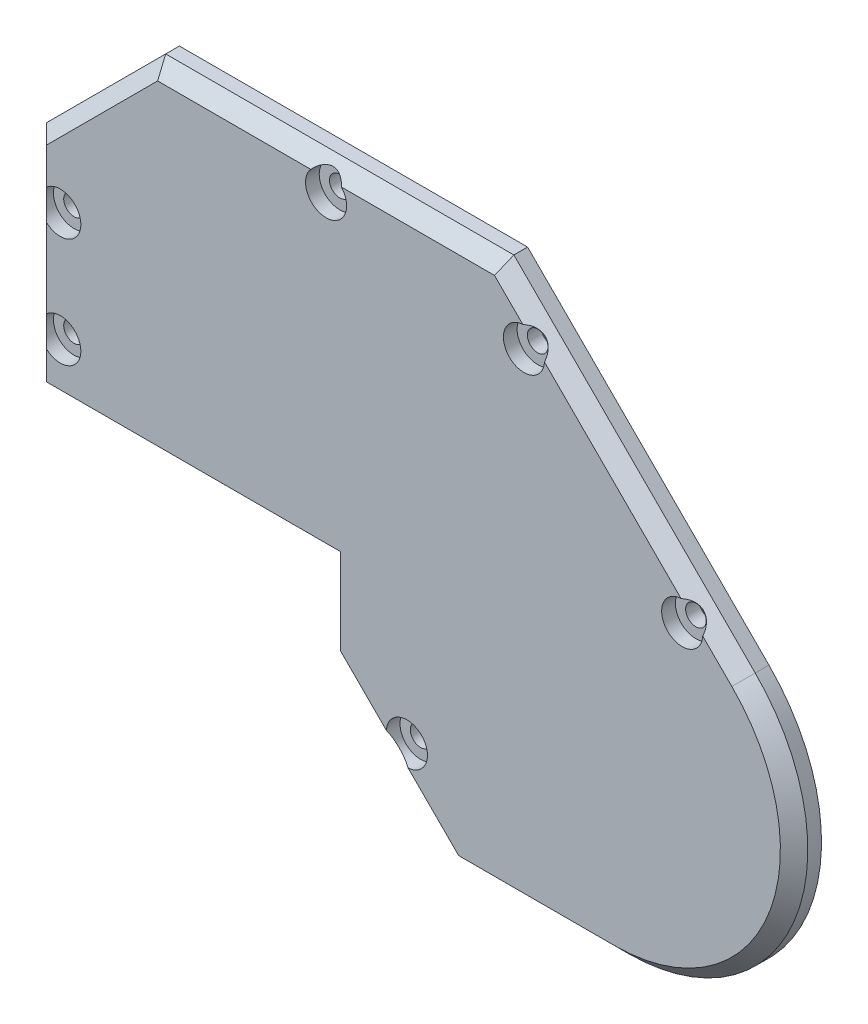
SolidWorks part; units mm, degrees
ref_plane "Plano frontal" through (0, 0, 0) normal (0, 0, 1) x (1, 0, 0)
ref_plane "Plano superior" through (0, 0, 0) normal (0, 1, 0) x (1, 0, 0)
ref_plane "Plano direito" through (0, 0, 0) normal (1, 0, 0) x (0, 0, -1)
sketch "Model" plane through (0, 0, 0) normal (0, 0, 1) x (1, 0, 0)
  line L0 (0, 0) -> (39, 0) construction
  line L1 (-0.7, 2.5) -> (39, 2.5)
  line L2 (39.7, 0) -> (39.7, -6.8548) construction
  line L3 (0, 0) -> (0, 31.4419) construction
  line L4 (50.1111, 46.949) -> (15.5071, 46.949) construction
  line L5 (0, 31.4419) -> (15.5071, 46.949) construction
  line L6 (42.2, -9.3548) -> (52.4452, -19.6) construction
  line L7 (39, -7.1448) -> (51.9502, -20.095) construction
  line L8 (97.9635, 12.6635) -> (63.6779, 46.949) construction
  line L9 (50.1111, 46.949) -> (63.6779, 46.949) construction
  line L10 (52.4452, -19.6) -> (59.4452, -26.6) construction
  line L11 (81.7, -26.6) -> (59.4452, -26.6) construction
  line L12 (-0.7, 0) -> (39, 0)
  line L13 (-0.7, 0) -> (-3.2, 0)
  line L14 (42.2, -10.3448) -> (51.9502, -20.095)
  line L15 (51.9502, -20.095) -> (59.1552, -27.3)
  line L16 (81.7, -27.3) -> (59.1552, -27.3)
  line L17 (98.4584, 13.1584) -> (63.9678, 47.649)
  line L18 (50.1111, 47.649) -> (63.9678, 47.649)
  line L19 (50.1111, 47.649) -> (15.2171, 47.649)
  line L20 (-0.7, 31.7319) -> (15.2171, 47.649)
  line L21 (-0.7, 2.5) -> (-0.7, 31.7319)
  line L22 (0, 0) -> (-0.7, 0) construction
  line L23 (38.8515, -10.5318) -> (50.1824, -21.8627) construction
  line L24 (-3.2, 0) -> (-3.2, 5)
  line L25 (-0.7, -0.7) -> (-0.7, 31.7319) construction
  line L26 (-0.7, -0.7) -> (39, -0.7) construction
  line L27 (39, -0.7) -> (39, -7.1448) construction
  line L28 (39, -0.7) -> (39, -0.7) construction
  line L29 (39, 0) -> (39.7, 0)
  line L30 (39.7, 0) -> (39.7, -11.3803)
  line L31 (39, 2.5) -> (39.7, 2.5)
  line L32 (39.7, 2.5) -> (42.2, 2.5)
  line L33 (39, 0) -> (39.7, 0) construction
  line L34 (42.2, 2.5) -> (42.2, -10.3448)
  line L35 (-3.2, 5) -> (-3.2, 32.7674)
  line L36 (-3.2, 32.7674) -> (14.1816, 50.149)
  line L37 (50.1111, 50.149) -> (14.1816, 50.149)
  line L38 (50.1111, 50.149) -> (65.0034, 50.149)
  line L39 (100.2262, 14.9262) -> (65.0034, 50.149)
  line L40 (81.7, -29.8) -> (58.1197, -29.8)
  line L41 (50.1824, -21.8627) -> (58.1197, -29.8)
  line L42 (39.7, -11.3803) -> (50.1824, -21.8627)
  line L43 (-0.7, 2.5) -> (-5.7, 2.5) construction
  line L44 (-5.7, 0) -> (-5.7, 2.5) construction
  line L45 (-0.7, 0) -> (-5.7, 0) construction
  line L46 (-3.2, 5) -> (-8.2, 5) construction
  line L47 (-8.2, -2.5) -> (-8.2, 5) construction
  line L48 (-0.7, -2.5) -> (39, -2.5) construction
  line L49 (-0.7, -2.5) -> (-8.2, -2.5) construction
  line L51 (40.6192, -8.764) -> (51.9502, -20.095) construction
  line L52 (39.7, -6.8548) -> (52.4452, -19.6) construction
  arc A0 (81.7, -27.3) -> (98.4584, 13.1584) centre (81.7, -3.6) ccw
  arc A1 (81.7, -29.8) -> (100.2262, 14.9262) centre (81.7, -3.6) ccw
  circle A2 centre (59.0726, 19.0274) radius 7.35 construction
  arc A5 (81.7, -26.6) -> (97.9635, 12.6635) centre (81.7, -3.6) ccw construction
  circle A6 centre (81.7, -3.6) radius 7.3 construction
  circle A13 centre (27.384, 23.481) radius 7.35 construction
  dimension "D2" = 2.5
  dimension "D1" = 0.7
extrude "Ressalto-extrusão1" add sketch "Model" along normal blind 48
sketch "Esboço12" plane through (57.5762, 57.5762, 0) normal (0.7071, 0.7071, 0) x (0, 0, -1)
  line L0 (-48, -35.4099) -> (-44, -35.4099) construction
  line L1 (-48, -60.3162) -> (-48, -10.5036) construction
  line L2 (-44, -35.4099) -> (-44, -43.4099) construction
  line L3 (-44, -35.4099) -> (-44, -19.4099) construction
  line L4 (-44, -19.4099) -> (-44, -51.4099) construction
  circle A0 centre (-44, -19.4099) radius 1.5
  circle A1 centre (-44, -51.4099) radius 1.5
extrude "Corte-extrusão10" cut sketch "Esboço12" against normal blind 10
sketch "Esboço13" plane through (0, 50.149, 0) normal (0, 1, 0) x (1, 0, 0)
  line L0 (39.5925, -48) -> (39.5925, -44) construction
  line L1 (65.0034, -48) -> (14.1816, -48) construction
  circle A0 centre (39.5925, -44) radius 1.5
extrude "Corte-extrusão11" cut sketch "Esboço13" against normal blind 10
sketch "Esboço14" plane through (-3.2, 0, 0) normal (-1, 0, 0) x (0, 0, 1)
  line L0 (48, 16.3837) -> (44, 16.3837) construction
  line L1 (48, 32.7674) -> (48, 0) construction
  line L2 (44, 16.3837) -> (44, 24.3837) construction
  line L3 (44, 24.3837) -> (44, 8.3837) construction
  circle A0 centre (44, 24.3837) radius 1.5
  circle A1 centre (44, 8.3837) radius 1.5
extrude "Corte-extrusão12" cut sketch "Esboço14" against normal blind 10
sketch "Esboço15" plane through (14.1598, 14.1598, 0) normal (-0.7071, -0.7071, 0) x (0, 0, 1)
  line L0 (48, -62.1686) -> (44, -62.1686) construction
  line L1 (48, -62.1686) -> (0, -62.1686) construction
  line L2 (0, -36.4548) -> (0, -50.9436) construction
  line L3 (0, -50.9436) -> (0, -60.8431) construction
  line L4 (0, -36.4548) -> (0, -50.9436) construction
  line L5 (0, -50.9436) -> (0, -60.8431) construction
  line L6 (0, -60.8431) -> (0, -36.4548) construction
  line L7 (0, -36.4548) -> (0, -48.6489) construction
  line L8 (0, -48.6489) -> (48, -48.6489) construction
  line L9 (48, -36.1192) -> (48, -62.1686) construction
  line L10 (48, -48.6489) -> (44, -48.6489) construction
  circle A0 centre (44, -48.6489) radius 1.5
extrude "Corte-extrusão13" cut sketch "Esboço15" against normal blind 10
sketch "Esboço16" plane through (0, 0, 48) normal (0, 0, 1) x (1, 0, 0)
  line L0 (39.7, 0) -> (39.7, -2)
  line L4 (42.2, -2) -> (42.2, 2.5)
  line L5 (42.2, 2.5) -> (-0.7, 2.5)
  line L6 (39.7, 0) -> (39.7, -2) construction
  line L8 (39.7, -2) -> (42.2, -2)
  line L12 (-0.7, 0) -> (39.7, 0)
  line L13 (-0.7, 2.5) -> (-0.7, 0)
extrude "Corte-extrusão14" cut sketch "Esboço16" against normal blind 10
sketch "Esboço17" plane through (0, 0, 0) normal (0, 0, -1) x (-1, 0, 0)
  line L0 (-92.8678, 22.2846) -> (-94.9892, 20.1632) construction
  line L1 (-92.8678, 22.2846) -> (-94.9892, 20.1632) construction
  line L2 (-70.2404, 44.912) -> (-72.3617, 42.7907) construction
  line L3 (-70.2404, 44.912) -> (-72.3617, 42.7907) construction
  line L4 (-38.0925, 50.149) -> (-41.0925, 50.149) construction
  line L5 (-38.0925, 50.149) -> (-41.0925, 50.149) construction
  line L6 (3.2, 22.8837) -> (3.2, 25.8837) construction
  line L7 (3.2, 22.8837) -> (3.2, 25.8837) construction
  line L8 (3.2, 6.8837) -> (3.2, 9.8837) construction
  line L9 (3.2, 6.8837) -> (3.2, 9.8837) construction
  line L10 (-49.6205, -21.3008) -> (-47.4992, -19.1795) construction
  line L11 (-49.6205, -21.3008) -> (-47.4992, -19.1795) construction
  line L12 (-93.9285, 21.2239) -> (-91.1001, 18.3955) construction
  line L13 (-71.3011, 43.8513) -> (-68.4727, 41.0229) construction
  line L14 (-39.5925, 50.149) -> (-39.5925, 46.149) construction
  line L15 (3.2, 24.3837) -> (-0.8, 24.3837) construction
  line L16 (3.2, 8.3837) -> (-0.8, 8.3837) construction
  line L17 (-48.5598, -20.2402) -> (-51.3883, -17.4117) construction
  line L18 (-69.8727, 39.6229) -> (-67.0727, 39.6229)
  line L19 (-92.5001, 19.7955) -> (-89.7001, 19.7955)
  line L20 (-92.5001, 19.7955) -> (-92.5001, 16.9955)
  line L21 (-92.5001, 16.9955) -> (-89.7001, 16.9955)
  line L22 (-89.7001, 19.7955) -> (-89.7001, 16.9955)
  line L23 (-92.5001, 19.7955) -> (-89.7001, 16.9955) construction
  line L24 (-92.5001, 16.9955) -> (-89.7001, 19.7955) construction
  line L25 (-69.8727, 39.6229) -> (-67.0727, 42.4229) construction
  line L26 (-69.8727, 42.4229) -> (-67.0727, 39.6229) construction
  line L27 (-69.8727, 42.4229) -> (-69.8727, 39.6229)
  line L28 (-69.8727, 42.4229) -> (-67.0727, 42.4229)
  line L29 (-67.0727, 42.4229) -> (-67.0727, 39.6229)
  line L30 (-38.1925, 47.549) -> (-38.1925, 44.749)
  line L31 (-40.9925, 44.749) -> (-38.1925, 47.549) construction
  line L32 (-40.9925, 47.549) -> (-40.9925, 44.749)
  line L33 (-40.9925, 47.549) -> (-38.1925, 44.749) construction
  line L34 (-40.9925, 44.749) -> (-38.1925, 44.749)
  line L35 (-40.9925, 47.549) -> (-38.1925, 47.549)
  line L36 (-2.2, 25.7837) -> (0.6, 22.9837) construction
  line L37 (-2.2, 22.9837) -> (0.6, 22.9837)
  line L38 (0.6, 25.7837) -> (0.6, 22.9837)
  line L39 (-2.2, 25.7837) -> (0.6, 25.7837)
  line L40 (-2.2, 22.9837) -> (0.6, 25.7837) construction
  line L41 (-2.2, 25.7837) -> (-2.2, 22.9837)
  line L42 (0.6, 9.7837) -> (0.6, 6.9837)
  line L43 (-2.2, 9.7837) -> (0.6, 9.7837)
  line L44 (-2.2, 6.9837) -> (0.6, 6.9837)
  line L45 (-2.2, 9.7837) -> (0.6, 6.9837) construction
  line L46 (-2.2, 9.7837) -> (-2.2, 6.9837)
  line L47 (-2.2, 6.9837) -> (0.6, 9.7837) construction
  line L48 (-52.7883, -18.8117) -> (-49.9883, -18.8117)
  line L49 (-52.7883, -16.0117) -> (-49.9883, -18.8117) construction
  line L50 (-52.7883, -18.8117) -> (-49.9883, -16.0117) construction
  line L51 (-52.7883, -16.0117) -> (-49.9883, -16.0117)
  line L52 (-49.9883, -16.0117) -> (-49.9883, -18.8117)
  line L53 (-52.7883, -16.0117) -> (-52.7883, -18.8117)
  circle A0 centre (-91.1001, 18.3955) radius 4
  circle A1 centre (-68.4727, 41.0229) radius 4
  circle A2 centre (-39.5925, 46.149) radius 4
  circle A3 centre (-0.8, 24.3837) radius 4
  circle A4 centre (-0.8, 8.3837) radius 4
  circle A5 centre (-51.3883, -17.4117) radius 4
extrude "Ressalto-extrusão2" add sketch "Esboço17" against normal blind 4
sketch "Esboço18" plane through (0, 0, 0) normal (0, 0, -1) x (-1, 0, 0)
  line L0 (-65.0034, 50.149) -> (-14.1816, 50.149) construction
  line L1 (-100.2262, 14.9262) -> (-65.0034, 50.149) construction
  line L2 (-14.1816, 50.149) -> (3.2, 32.7674) construction
  line L3 (3.2, 32.7674) -> (3.2, 0) construction
  line L4 (3.2, 0) -> (-39.7, 0) construction
  line L5 (-39.7, 0) -> (-39.7, -11.3803) construction
  line L6 (-39.7, -11.3803) -> (-58.1197, -29.8) construction
  line L7 (-58.1197, -29.8) -> (-81.7, -29.8) construction
  line L8 (-65.0034, 50.149) -> (-14.1816, 50.149)
  line L9 (-100.2262, 14.9262) -> (-65.0034, 50.149)
  line L10 (-14.1816, 50.149) -> (3.2, 32.7674)
  line L11 (3.2, 32.7674) -> (3.2, 0)
  line L12 (3.2, 0) -> (-39.7, 0)
  line L13 (-39.7, 0) -> (-39.7, -11.3803)
  line L14 (-39.7, -11.3803) -> (-58.1197, -29.8)
  line L15 (-58.1197, -29.8) -> (-81.7, -29.8)
  line L16 (-90.1687, 16.5268) -> (-90.1687, 19.3268) construction
  line L17 (-90.1687, 19.3268) -> (-92.29, 19.3268) construction
  line L18 (-90.1687, 16.5268) -> (-90.1687, 19.3268) construction
  line L19 (-90.1687, 19.3268) -> (-92.29, 19.3268) construction
  line L20 (-90.1687, 16.5268) -> (-92.6294, 18.9875) construction
  line L21 (-92.9687, 18.6482) -> (-92.29, 19.3268) construction
  line L22 (-90.1687, 19.3268) -> (-92.9687, 16.5268) construction
  arc A0 (-100.2262, 14.9262) -> (-81.7, -29.8) centre (-81.7, -3.6) ccw construction
  arc A1 (-100.2262, 14.9262) -> (-81.7, -29.8) centre (-81.7, -3.6) ccw
  circle A2 centre (-91.5687, 17.9268) radius 1.5
  circle A3 centre (-68.4727, 41.0229) radius 1.5
  circle A4 centre (-39.5925, 46.149) radius 1.5
  circle A5 centre (-0.8, 24.3837) radius 1.5
  circle A6 centre (-51.3883, -17.4117) radius 1.5
  circle A7 centre (-0.8, 8.3837) radius 1.5
extrude "Ressalto-extrusão3" add sketch "Esboço18" along normal blind 4
chamfer "Chanfro1" distance 2 angle 45 9 edges at (39.5925, 50.149, -4) (5.4908, 41.4582, -4) (-3.2, 16.3837, -4) (18.25, 0, -4) (39.7, -5.6902, -4) (48.9098, -20.5902, -4) (69.9098, -29.8, -4) (105.9056, -13.6263, -4) (82.6148, 32.5376, -4)
sketch "Esboço19" plane through (0, 0, 48) normal (0, 0, 1) x (1, 0, 0)
  line L8 (65.0034, 50.149) -> (14.1816, 50.149)
  line L9 (14.1816, 50.149) -> (-3.2, 32.7674)
  line L10 (-3.2, 32.7674) -> (-3.2, 0)
  line L11 (-3.2, 0) -> (39.7, 0)
  line L12 (39.7, 0) -> (39.7, -11.3803)
  line L13 (39.7, -11.3803) -> (58.1197, -29.8)
  line L14 (58.1197, -29.8) -> (81.7, -29.8)
  line L15 (100.2262, 14.9262) -> (65.0034, 50.149)
  line L16 (65.0034, 50.149) -> (14.1816, 50.149)
  line L17 (14.1816, 50.149) -> (-3.2, 32.7674)
  line L18 (-3.2, 32.7674) -> (-3.2, 0)
  line L19 (-3.2, 0) -> (39.7, 0)
  line L20 (39.7, 0) -> (39.7, -11.3803)
  line L21 (39.7, -11.3803) -> (58.1197, -29.8)
  line L22 (58.1197, -29.8) -> (81.7, -29.8)
  line L23 (100.2262, 14.9262) -> (65.0034, 50.149)
  arc A5 (81.7, -29.8) -> (100.2262, 14.9262) centre (81.7, -3.6) ccw
  arc A6 (81.7, -29.8) -> (100.2262, 14.9262) centre (81.7, -3.6) ccw
  dimension "D3" = 0
extrude "Corte-extrusão15" cut sketch "Esboço19" against normal up to surface (48 mm away) up to face at (43.9312, 14.8678, 0)
sketch "Esboço20" plane through (0, 0, -4) normal (0, 0, -1) x (-1, 0, 0)
  circle A0 centre (-0.8, 24.3837) radius 3
  circle A1 centre (-0.8, 8.3837) radius 3
  circle A2 centre (-39.5925, 46.149) radius 3
  circle A3 centre (-68.4727, 41.0229) radius 3
  circle A4 centre (-51.3883, -17.4117) radius 3
  circle A5 centre (-91.5687, 17.9268) radius 3
extrude "Corte-extrusão16" cut sketch "Esboço20" against normal blind 2
sketch "Esboço21" plane through (0, 0, 0) normal (0, 0, 1) x (1, 0, 0)
  line L8 (100.2262, 14.9262) -> (65.0034, 50.149)
  line L9 (65.0034, 50.149) -> (14.1816, 50.149)
  line L10 (14.1816, 50.149) -> (-3.2, 32.7674)
  line L11 (-3.2, 32.7674) -> (-3.2, 0)
  line L12 (-3.2, 0) -> (39.7, 0)
  line L13 (39.7, 0) -> (39.7, -11.3803)
  line L14 (39.7, -11.3803) -> (58.1197, -29.8)
  line L15 (58.1197, -29.8) -> (81.7, -29.8)
  line L16 (100.2262, 14.9262) -> (65.0034, 50.149)
  line L17 (65.0034, 50.149) -> (14.1816, 50.149)
  line L18 (14.1816, 50.149) -> (-3.2, 32.7674)
  line L19 (-3.2, 32.7674) -> (-3.2, 0)
  line L20 (-3.2, 0) -> (39.7, 0)
  line L21 (39.7, 0) -> (39.7, -11.3803)
  line L22 (39.7, -11.3803) -> (58.1197, -29.8)
  line L23 (58.1197, -29.8) -> (81.7, -29.8)
  arc A1 (81.7, -29.8) -> (100.2262, 14.9262) centre (81.7, -3.6) ccw
  arc A2 (81.7, -29.8) -> (100.2262, 14.9262) centre (81.7, -3.6) ccw
  dimension "D1" = 0
mirror "Espelhar1" about plane through (81.7, -3.6, 0) normal (0, 0, -1) of bodies 120
extrude "Corte-extrusão17" cut sketch "Esboço21" against normal blind 10
